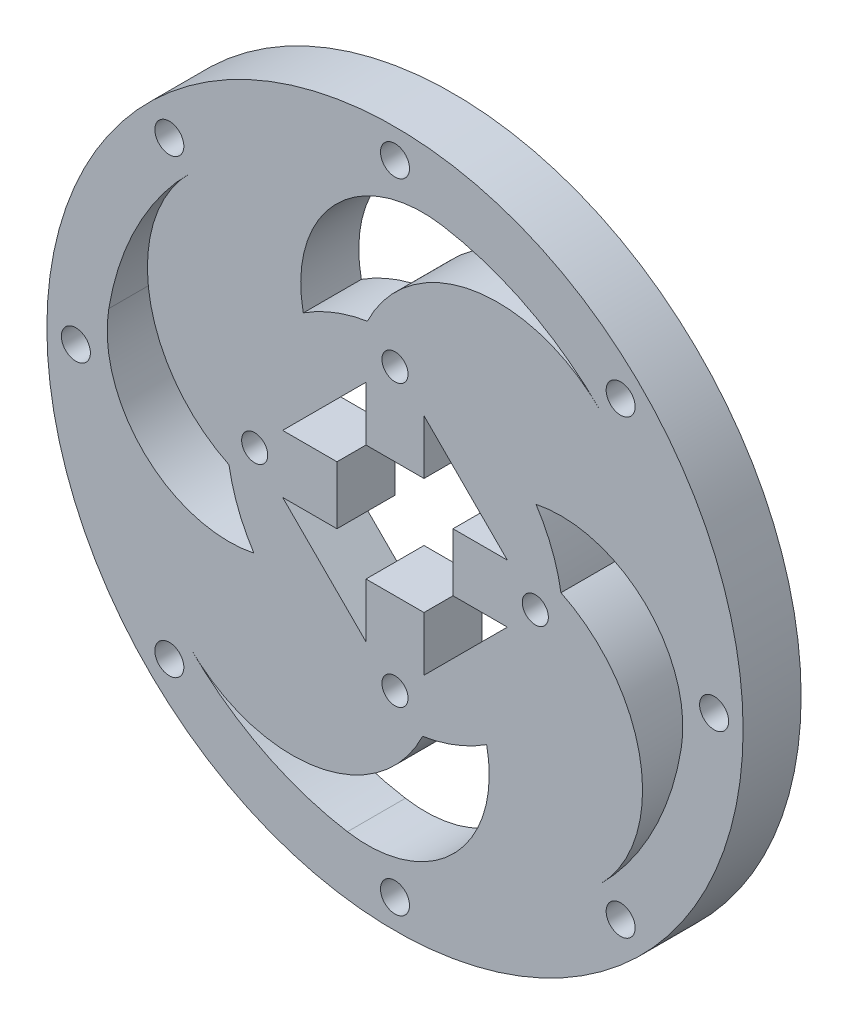
SolidWorks part; units mm, degrees
ref_plane "Front Plane" through (0, 0, 0) normal (0, 0, 1) x (1, 0, 0)
ref_plane "Top Plane" through (0, 0, 0) normal (0, 1, 0) x (1, 0, 0)
ref_plane "Right Plane" through (0, 0, 0) normal (1, 0, 0) x (0, 0, -1)
sketch "Sketch6" plane through (0, 0, 0) normal (0, 0, 1) x (1, 0, 0)
  circle A0 centre (0, 0) radius 20
  circle A1 centre (0, 0) radius 29
  dimension "D1" = 40
  dimension "D2" = 58
extrude "Inner Ring" add sketch "Sketch6" against normal blind 10 separate body
sketch "Sketch7" plane through (0, 0, 0) normal (0, 0, 1) x (1, 0, 0)
  line L2 (-10, 5) -> (-10, -5)
  line L3 (-5, 10) -> (5, 10)
  line L4 (10, 5) -> (10, -5)
  line L5 (-5, -10) -> (5, -10)
  line L14 (-19.3649, 5) -> (-10, 5)
  line L15 (-19.3649, -5) -> (-10, -5)
  line L16 (-5, 19.3649) -> (-5, 10)
  line L17 (5, 19.3649) -> (5, 10)
  line L18 (19.3649, 5) -> (10, 5)
  line L19 (19.3649, -5) -> (10, -5)
  line L20 (5, -19.3649) -> (5, -10)
  line L21 (-5, -19.3649) -> (-5, -10)
  circle A1 centre (0, 0) radius 20
  circle M19 centre (0, 0) radius 20
  dimension "D1" = 20
  dimension "D2" = 20
  dimension "D3" = 10
  dimension "D5" = 10
  dimension "D7" = 10
  dimension "D8" = 10
extrude "Motor Connector Cut" add sketch "Sketch7" against normal blind 10 contours L19 L18 L4 M19 | L17 L16 L3 M19 | L15 L2 L14 M19 | L21 L20 L5 M19
sketch "Sketch8" plane through (0, 0, 0) normal (0, 0, 1) x (1, 0, 0)
  circle A1 centre (0, 24.1825) radius 2.25
  circle A2 centre (24.1825, 0) radius 2.25
  circle A3 centre (0, -24.1825) radius 2.25
  circle A4 centre (-24.1825, 0) radius 2.25
  dimension "D1" = 4.5
  dimension "D2" = 4.5
  dimension "D3" = 4.5
  dimension "D4" = 4.5
  dimension "D6" = 48.3649
  dimension "D8" = 48.3649
extrude "Motor Connector Holes" cut sketch "Sketch8" against normal blind 18 and the other way blind 1
sketch "Sketch9" plane through (0, 0, 0) normal (0, 0, 1) x (1, 0, 0)
  circle A0 centre (0, 0) radius 50
  circle A1 centre (0, 0) radius 60
  circle A2 centre (0, 55) radius 2.5
  circle A3 centre (0, 55) radius 1.5
  circle A4 centre (-38.8909, 38.8909) radius 1.5
  circle A5 centre (-55, 0) radius 1.5
  circle A6 centre (-38.8909, -38.8909) radius 1.5
  circle A7 centre (0, -55) radius 1.5
  circle A8 centre (38.8909, -38.8909) radius 1.5
  circle A9 centre (55, 0) radius 1.5
  circle A10 centre (38.8909, 38.8909) radius 1.5
  circle A11 centre (-38.8909, 38.8909) radius 2.5
  circle A12 centre (-55, 0) radius 2.5
  circle A13 centre (-38.8909, -38.8909) radius 2.5
  circle A14 centre (0, -55) radius 2.5
  circle A15 centre (38.8909, -38.8909) radius 2.5
  circle A16 centre (55, 0) radius 2.5
  circle A17 centre (38.8909, 38.8909) radius 2.5
  dimension "D1" = 120
  dimension "D2" = 100
  dimension "D3" = 3
  dimension "D4" = 3
  dimension "D5" = 3
  dimension "D6" = 3
  dimension "D7" = 3
  dimension "D8" = 3
  dimension "D9" = 3
  dimension "D10" = 3
  dimension "D11" = 5
  dimension "D12" = 5
  dimension "D13" = 5
  dimension "D14" = 5
  dimension "D15" = 5
  dimension "D16" = 5
  dimension "D17" = 5
  dimension "D18" = 5
sketch "Sketch10" plane through (0, 0, 0) normal (0, 0, 1) x (1, 0, 0)
  circle A0 centre (0, 0) radius 29
  circle A1 centre (0, 29) radius 21
  circle A2 centre (29, 0) radius 21
  circle A3 centre (0, -29) radius 21
  circle A4 centre (-29, 0) radius 21
  circle A5 centre (0, 0) radius 50
  circle A6 centre (-17.7016, 17.7016) radius 24.9662
  circle A7 centre (17.7016, 17.7016) radius 24.9662
  circle A8 centre (17.7016, -17.7016) radius 24.9662
  circle A9 centre (-17.7016, -17.7016) radius 24.9662
  circle A10 centre (-28.6072, 4.7568) radius 21
  circle A11 centre (-28.6072, -4.7568) radius 21
  circle A12 centre (-4.7568, -28.6072) radius 21
  circle A13 centre (4.7568, -28.6072) radius 21
  circle A14 centre (28.6072, -4.7568) radius 21
  circle A15 centre (28.6072, 4.7568) radius 21
  circle A16 centre (4.7568, 28.6072) radius 21
  circle A17 centre (-4.7568, 28.6072) radius 21
extrude "Middle Pattern" add sketch "Sketch10" against normal blind 10 contours A0 A10 A1 | A16 A6 A1 A10 A0 | A10 A17 A4 A0 A1 | A6 A17 A10 A1 | A1 A17 A6 | A16 A17 A1 A6 | A17 A16 A1 | A16 A5 A1 | A2 A16 A15 A1 A0 | A0 A16 A2 | A16 A0 A14 A7 A2 | A16 A2 A7 A15 | A15 A7 A2 | A14 A15 A2 A7 | A15 A14 A2 | A1 A15 A0 | A2 A13 A0 | A3 A14 A13 A2 A0 | A0 A14 A3 | A14 A0 A12 A8 A3 | A14 A3 A8 A13 | A12 A13 A3 A8 | A3 A13 A8 | A13 A12 A3 | A13 A3 A5 | A15 A2 A5 | A17 A1 A5 | A12 A0 A10 A9 A4 | A4 A12 A11 A3 A0 | A0 A12 A4 | A12 A4 A9 A11 | A4 A11 A9 | A10 A11 A4 A9 | A11 A4 A5 | A11 A10 A4 | A4 A17 A0 | A0 A17 A7 A6 | A17 A0 A15 A1 A7 | A15 A16 A7 A1 | A16 A15 A7 | A15 A5 A7 | A0 A15 A8 A7 | A15 A0 A13 A2 A8 | A13 A14 A8 A2 | A14 A13 A8 | A7 A8 A0 | A6 A7 A0 | A13 A5 A8 | A11 A5 A9 | A12 A11 A9 | A11 A12 A9 A3 | A13 A0 A11 A3 A9 | A0 A13 A9 A8 | A3 A11 A0 | A8 A9 A0 | A17 A4 A6 A11 A0 | A17 A10 A6 A4 | A17 A6 A10 | A0 A11 A6 A9 | A0 A9 A6 | A17 A5 A6 | A12 A5 A3 | A10 A5 A4 | A14 A5 A2
extrude "Boss-Extrude1" add sketch "Sketch9" against normal blind 10 contours A1 A17 A16 A15 A14 A13 A12 A11 A2 A0 | A3 | A10
sketch "Sketch11" plane through (0, 0, 0) normal (0, 0, 1) x (1, 0, 0)
  line L0 (-19.3649, 5) -> (-5, 19.3649)
  line L1 (5, 19.3649) -> (19.3649, 5)
  line L2 (19.3649, -5) -> (5, -19.3649)
  line L3 (-5, -19.3649) -> (-19.3649, -5)
  arc A0 (19.3649, 5) -> (5, 19.3649) centre (0, 0) ccw
  arc A1 (5, -19.3649) -> (19.3649, -5) centre (0, 0) ccw
  arc A2 (-19.3649, -5) -> (-5, -19.3649) centre (0, 0) ccw
  arc A3 (-5, 19.3649) -> (-19.3649, 5) centre (0, 0) ccw
extrude "Boss-Extrude2" add sketch "Sketch11" against normal blind 10
